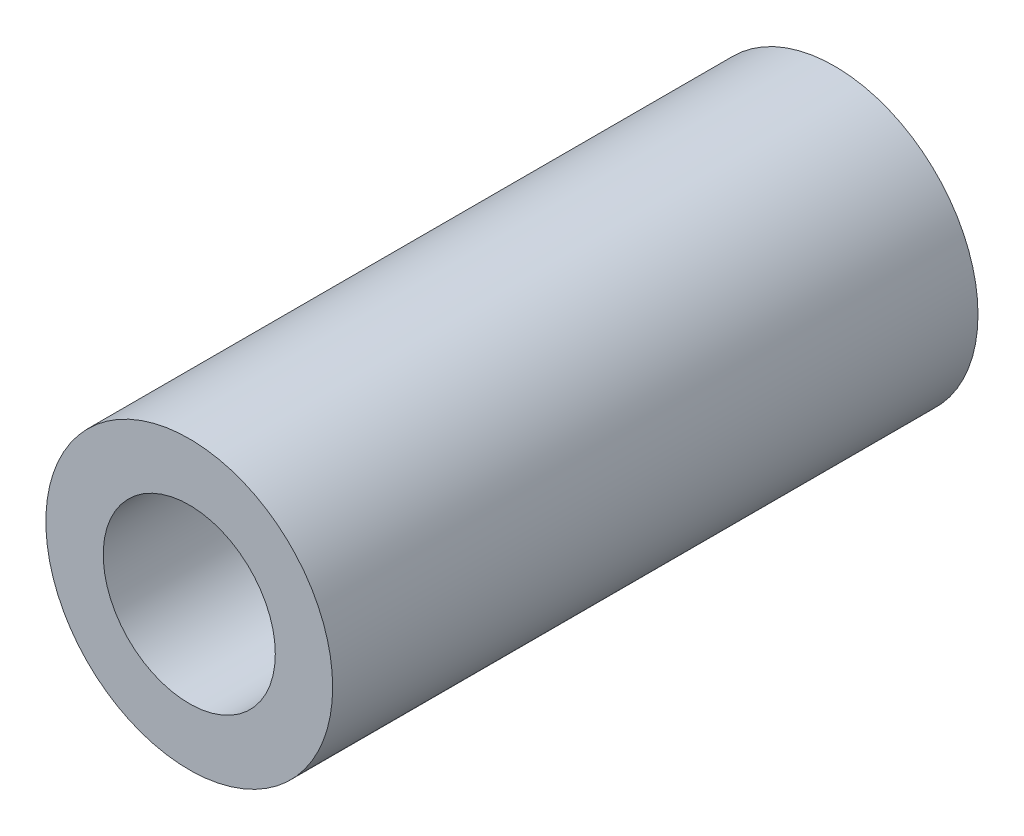
SolidWorks part; units mm, degrees
material "Copper"
ref_plane "Front Plane" through (0, 0, 0) normal (0, 0, 1) x (1, 0, 0)
ref_plane "Top Plane" through (0, 0, 0) normal (0, 1, 0) x (1, 0, 0)
ref_plane "Right Plane" through (0, 0, 0) normal (1, 0, 0) x (0, 0, -1)
sketch "Sketch1" plane through (0, 0, 0) normal (0, 0, 1) x (1, 0, 0)
  circle A0 centre (0, 0) radius 6
  circle A1 centre (0, 0) radius 10
  dimension "D1" = 12
  dimension "D2" = 20
extrude "Boss-Extrude1" add sketch "Sketch1" along normal blind 45
